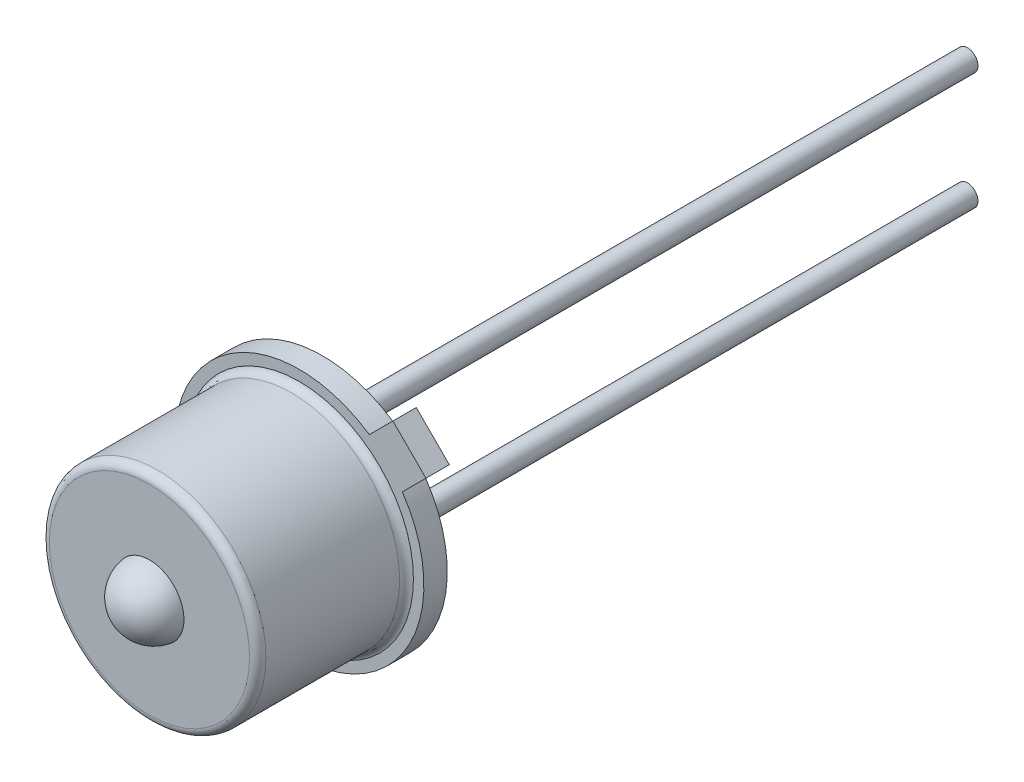
SolidWorks part; units mm, degrees
ref_plane "Front Plane" through (0, 0, 0) normal (0, 0, 1) x (1, 0, 0)
ref_plane "Top Plane" through (0, 0, 0) normal (0, 1, 0) x (1, 0, 0)
ref_plane "Right Plane" through (0, 0, 0) normal (1, 0, 0) x (0, 0, -1)
sketch "Sketch1" plane through (0, 0, 0) normal (0, 0, 1) x (1, 0, 0)
  line L0 (0, 2.7051) -> (0, -2.7051) construction
  line L1 (0, -2.7051) -> (2.7051, 0) construction
  line L2 (2.7051, 0) -> (-2.7051, 0) construction
  line L3 (0, 0) -> (1.3525, -1.3525) construction
  line L4 (0, -2.7051) -> (-2.7051, 0) construction
  line L5 (-2.7051, 0) -> (0, 2.7051) construction
  line L6 (0, 2.7051) -> (2.7051, 0) construction
  line L7 (-1.9128, -1.9128) -> (2.391, 2.391) construction
  line L8 (2.7496, 2.0323) -> (2.0323, 2.7496)
  line L9 (2.0323, 2.7496) -> (1.5202, 2.2375)
  line L10 (2.7496, 2.0323) -> (2.2375, 1.5202)
  arc A0 (1.5202, 2.2375) -> (2.2375, 1.5202) centre (0, 0) ccw
  circle A1 centre (0, 0) radius 1.27 construction
  dimension "D1" = 5.4102
  dimension "D2" = 2.54
  dimension "D4" = 6.0865
  dimension "D5" = 0.5072
extrude "Boss-Extrude1" add sketch "Sketch1" along normal blind 0.5072
sketch "Sketch3" plane through (0, 0, 0.5072) normal (0, 0, 1) x (1, 0, 0)
  circle A0 centre (0, 0) radius 2.3495 construction
  dimension "D1" = 4.699
sketch "Sketch4" plane through (0, 0, 0) normal (1, 0, 0) x (0, 0, -1)
  line L0 (-0.6779, 2.3495) -> (-3.5814, 2.3495)
  line L1 (-0.5072, 2.3495) -> (-0.5072, -2.3495) construction
  line L2 (-0.5072, 2.0323) -> (-0.5072, 2.7496) construction
  line L3 (-3.7592, 0.7493) -> (-3.7592, 2.1717)
  line L4 (-3.7592, 0.7493) -> (-3.6068, 0.7493)
  line L5 (-3.6068, 0.7493) -> (-3.6068, 2.1971)
  line L6 (-3.6068, 2.1971) -> (-0.5072, 2.1971)
  line L7 (-0.5072, 2.1971) -> (-0.5072, 2.3503)
  line L8 (-0.5072, 2.3503) -> (-0.5072, 2.4776)
  line L9 (-0.5072, 0) -> (-4.2661, 0) construction
  arc A0 (-3.5814, 2.3495) -> (-3.7592, 2.1717) centre (-3.5814, 2.1717) ccw
  arc A1 (-0.5072, 2.4776) -> (-0.6779, 2.3495) centre (-0.6779, 2.5273) cw
  point P14 (-3.7592, 2.3495)
  dimension "D5" = 0.1778
  dimension "D1" = 3.252
  dimension "D2" = 1.6002
  dimension "D3" = 0.1524
  dimension "D4" = 0.1524
  dimension "D6" = 2.3495
revolve "Revolve1" add sketch "Sketch4" angle 360 about L9
sketch "Sketch7" plane through (0, 0, 0) normal (0, 0, -1) x (-1, 0, 0)
  line L0 (0, 2.7051) -> (0, -2.7051) construction
  line L1 (0, -2.7051) -> (-2.7051, 0) construction
  line L2 (-2.7051, 0) -> (0, 2.7051) construction
  line L3 (0, 2.7051) -> (2.7051, 0) construction
  line L4 (2.7051, 0) -> (0, -2.7051) construction
  line L5 (-2.7051, 0) -> (2.7051, 0) construction
  line L6 (-2.391, 2.391) -> (1.9128, -1.9128) construction
  line L7 (-2.7496, 2.0323) -> (-2.0323, 2.7496) construction
  arc A0 (-2.2375, 1.5202) -> (-1.5202, 2.2375) centre (0, 0) ccw construction
  circle A1 centre (0, 0) radius 1.27 construction
  circle A2 centre (0, -1.27) radius 0.2286
  circle A3 centre (1.27, 0) radius 0.2286
  circle A5 centre (0, 1.27) radius 0.2286
  dimension "D1" = 2.54
  dimension "D2" = 0.4572
extrude "Boss-Extrude2" add sketch "Sketch7" along normal blind 13.9954
sketch "Sketch8" plane through (0, 0, 0) normal (0, 0, -1) x (-1, 0, 0)
  circle A0 centre (1.2646, 0) radius 0.5072
  dimension "D1" = 1.0144
extrude "Boss-Extrude3" add sketch "Sketch8" along normal blind 0.3382
sketch "Sketch11" plane through (0, 0, 0) normal (0, 1, 0) x (1, 0, 0)
  line L0 (0.7493, -3.7592) -> (-0.7493, -3.7592) construction
  line L1 (0, -3.7592) -> (0, -4.4196) construction
  line L2 (0, -4.4196) -> (0, -4.2164)
  line L3 (-0.5439, -3.7592) -> (-0.7493, -3.7592)
  arc A0 (0, -4.4196) -> (-0.7493, -3.7592) centre (0, -3.6643) cw
  arc A1 (0, -4.2164) -> (-0.5439, -3.7592) centre (0, -3.6643) cw
  arc A2 (0, -4.2164) -> (-0.5477, -3.7337) centre (0, -3.6643) cw construction
  dimension "D1" = 0.6604
  dimension "D2" = 0.2032
revolve "Revolve3" add sketch "Sketch11" angle 360 about L1
